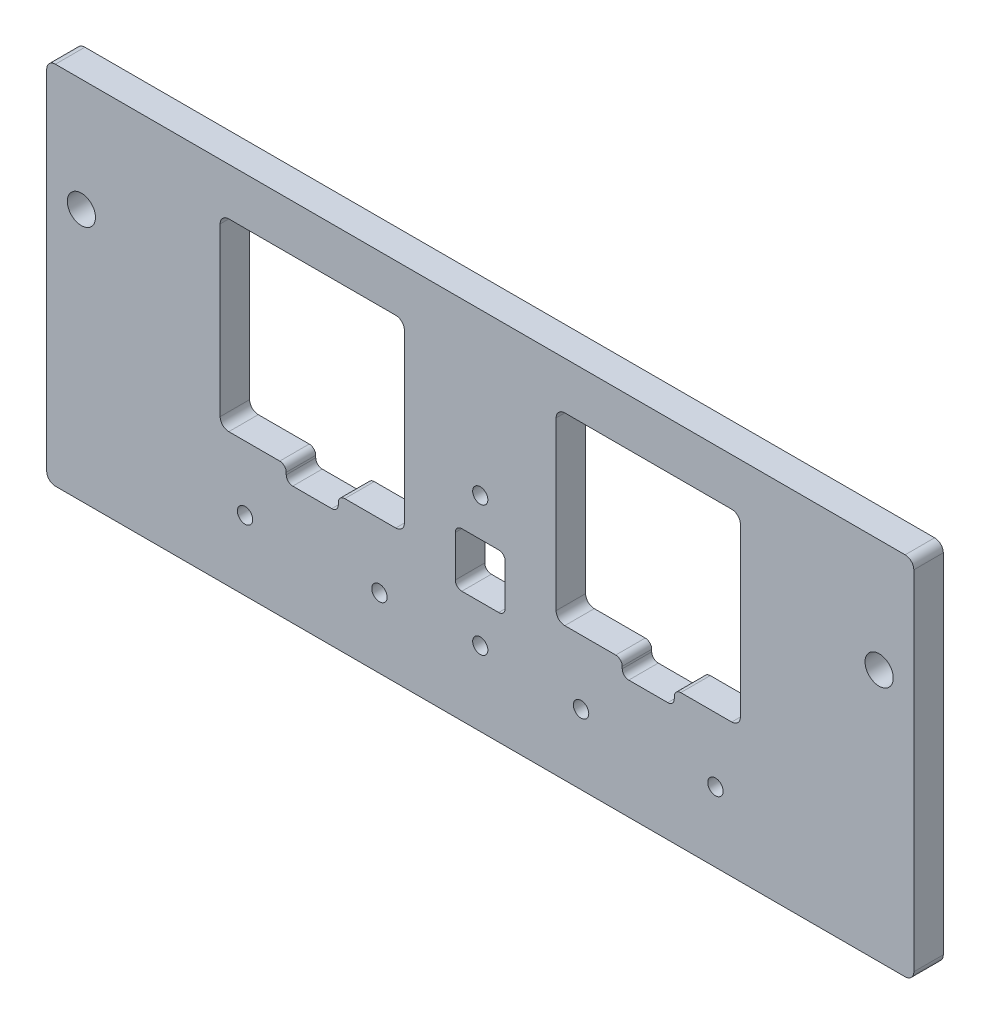
SolidWorks part; units mm, degrees
ref_plane "Front Plane" through (0, 0, 0) normal (0, 0, 1) x (1, 0, 0)
ref_plane "Top Plane" through (0, 0, 0) normal (0, 1, 0) x (1, 0, 0)
ref_plane "Right Plane" through (0, 0, 0) normal (1, 0, 0) x (0, 0, -1)
sketch "Sketch1" plane through (0, 0, 0) normal (0, 0, 1) x (1, 0, 0)
  line L1 (100, -42.15) -> (-100, -42.15)
  line L2 (100, -42.15) -> (100, 42.15)
  line L3 (100, 42.15) -> (-100, 42.15)
  line L4 (-100, -42.15) -> (-100, 42.15)
  line L5 (100, -42.15) -> (-100, 42.15) construction
  line L6 (100, 42.15) -> (-100, -42.15) construction
  point P0 (0, 0)
  dimension "D1" = 200
  dimension "D2" = 84.3
extrude "Boss-Extrude1" add sketch "Sketch1" along normal blind 6.8
sketch "Sketch2" plane through (0, 0, 6.8) normal (0, 0, 1) x (1, 0, 0)
  line L0 (100, 42.15) -> (-100, 42.15) construction
  line L1 (92, 16.15) -> (-92, 16.15) construction
  circle A0 centre (-92, 16.15) radius 3.25
  circle A1 centre (92, 16.15) radius 3.25
  point P10 (0, 16.15)
  dimension "D1" = 6.5
  dimension "D2" = 92
  dimension "D3" = 26
extrude "Cut-Extrude1" cut sketch "Sketch2" against normal blind 6.8
fillet "Fillet1" radius 2 4 edges at (100, 42.15, 3.4) (100, -42.15, 3.4) (-100, -42.15, 3.4) (-100, 42.15, 3.4)
sketch "Sketch3" plane through (0, 0, 6.8) normal (0, 0, 1) x (1, 0, 0)
  line L0 (100, -40.15) -> (100, 40.15) construction
  line L1 (60, -11.25) -> (17.5, -11.25)
  line L2 (60, -11.25) -> (60, 31.25)
  line L3 (60, 31.25) -> (17.5, 31.25)
  line L4 (17.5, -11.25) -> (17.5, 31.25)
  line L5 (60, -11.25) -> (17.5, 31.25) construction
  line L6 (60, 31.25) -> (17.5, -11.25) construction
  line L7 (54.25, -26.082) -> (23.25, -26.082) construction
  circle A0 centre (23.25, -26.082) radius 1.775
  circle A1 centre (54.25, -26.082) radius 1.775
  point P0 (38.75, 10)
  point P16 (38.75, -26.082)
  dimension "D6" = 3.55
  dimension "D1" = 42.5
  dimension "D2" = 40
  dimension "D3" = 10
  dimension "D4" = 14.832
  dimension "D5" = 31
extrude "Cut-Extrude2" cut sketch "Sketch3" against normal through all
fillet "Fillet2" radius 2 4 edges at (60, 31.25, 3.4) (17.5, 31.25, 3.4) (17.5, -11.25, 3.4) (60, -11.25, 3.4)
mirror "Mirror1" [suppressed] about plane through (0, 0, 0) normal (1, 0, 0)
sketch "Sketch4" plane through (0, 0, 6.8) normal (0, 0, 1) x (1, 0, 0)
  line L1 (44.75, -14.75) -> (32.75, -14.75)
  line L2 (44.75, -14.75) -> (44.75, -7.75)
  line L3 (44.75, -7.75) -> (32.75, -7.75)
  line L4 (32.75, -14.75) -> (32.75, -7.75)
  line L5 (44.75, -14.75) -> (32.75, -7.75) construction
  line L6 (44.75, -7.75) -> (32.75, -14.75) construction
  line L7 (19.5, -11.25) -> (58, -11.25) construction
  point P0 (38.75, -11.25)
  dimension "D1" = 3.5
  dimension "D2" = 12
extrude "Cut-Extrude3" cut sketch "Sketch4" against normal through all
fillet "Fillet3" radius 1.5 4 edges at (44.75, -14.75, 3.4) (32.75, -14.75, 3.4) (32.75, -11.25, 3.4) (44.75, -11.25, 3.4)
sketch "Sketch5" plane through (0, 0, 6.8) normal (0, 0, 1) x (1, 0, 0)
  line L0 (0, 5) -> (0, -25) construction
  line L1 (5.75, -16.25) -> (-5.75, -16.25)
  line L2 (5.75, -16.25) -> (5.75, -3.75)
  line L3 (5.75, -3.75) -> (-5.75, -3.75)
  line L4 (-5.75, -16.25) -> (-5.75, -3.75)
  line L5 (5.75, -16.25) -> (-5.75, -3.75) construction
  line L6 (5.75, -3.75) -> (-5.75, -16.25) construction
  circle A0 centre (0, -25) radius 1.75
  circle A1 centre (0, 5) radius 1.75
  point P0 (0, -10)
  point P10 (0, -10)
  dimension "D4" = 3.5
  dimension "D1" = 12.5
  dimension "D2" = 11.5
  dimension "D3" = 30
  dimension "D5" = 10
extrude "Cut-Extrude4" cut sketch "Sketch5" against normal through all
fillet "Fillet4" radius 1.5 4 edges at (-5.75, -3.75, 3.4) (5.75, -3.75, 3.4) (5.75, -16.25, 3.4) (-5.75, -16.25, 3.4)
mirror "Mirror2" about plane through (0, 0, 0) normal (1, 0, 0) of "Fillet2", "Cut-Extrude2", "Cut-Extrude3", "Fillet3"
